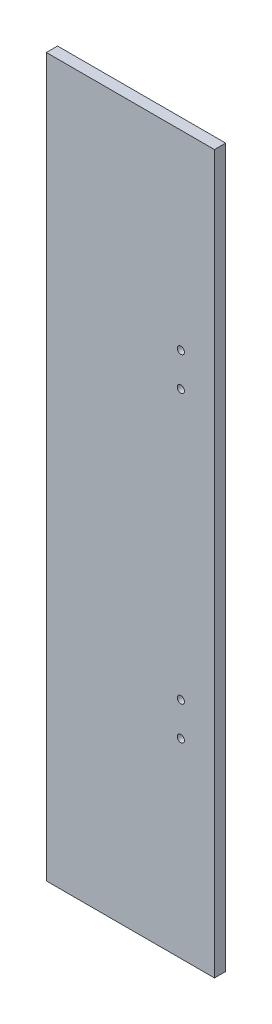
SolidWorks part; units mm, degrees
ref_plane "Front Plane" through (0, 0, 0) normal (0, 0, 1) x (1, 0, 0)
ref_plane "Top Plane" through (0, 0, 0) normal (0, 1, 0) x (1, 0, 0)
ref_plane "Right Plane" through (0, 0, 0) normal (1, 0, 0) x (0, 0, -1)
sketch "Sketch1" plane through (0, 0, 0) normal (0, 0, 1) x (1, 0, 0)
  line L1 (-37.5, -160) -> (37.5, -160)
  line L2 (-37.5, -160) -> (-37.5, 160)
  line L3 (-37.5, 160) -> (37.5, 160)
  line L4 (37.5, -160) -> (37.5, 160)
  line L5 (-37.5, -160) -> (37.5, 160) construction
  line L6 (-37.5, 160) -> (37.5, -160) construction
  point P0 (0, 0)
  dimension "D1" = 320
  dimension "D2" = 75
extrude "Boss-Extrude1" add sketch "Sketch1" along normal blind 5
sketch "Sketch2" plane through (0, 0, 0) normal (0, 0, -1) x (-1, 0, 0)
  line L0 (-37.5, 0) -> (-22.5, 0) construction
  line L1 (-37.5, -160) -> (-37.5, 160) construction
  line L2 (-22.5, 0) -> (-22.5, 60) construction
  line L3 (-22.5, 60) -> (-22.5, 75) construction
  circle A0 centre (-22.5, 75) radius 1.6
  circle A1 centre (-22.5, 60) radius 1.6
  circle A2 centre (-22.5, -60) radius 1.6
  circle A3 centre (-22.5, -75) radius 1.6
  dimension "D4" = 3.2
  dimension "D5" = 3.2
  dimension "D1" = 15
  dimension "D2" = 15
  dimension "D3" = 60
extrude "Cut-Extrude1" cut sketch "Sketch2" against normal up to next
